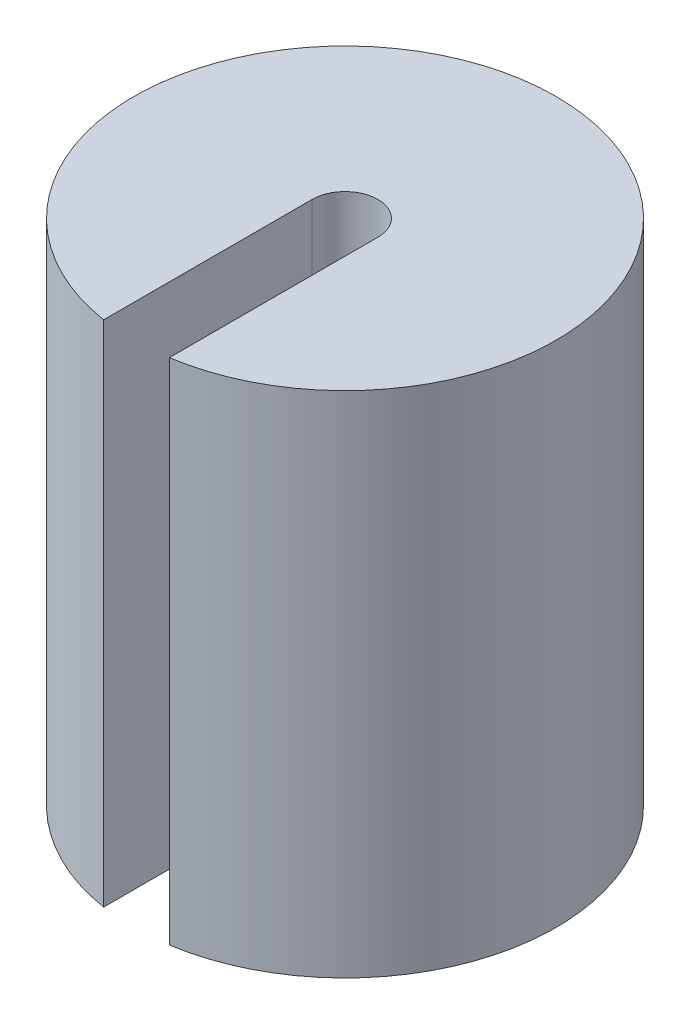
SolidWorks part; units mm, degrees
material "Brass"
ref_plane "Front Plane" through (0, 0, 0) normal (0, 0, 1) x (1, 0, 0)
ref_plane "Top Plane" through (0, 0, 0) normal (0, 1, 0) x (1, 0, 0)
ref_plane "Right Plane" through (0, 0, 0) normal (1, 0, 0) x (0, 0, -1)
sketch "Sketch1" plane through (0, 0, 0) normal (0, 1, 0) x (1, 0, 0)
  circle A0 centre (0, 0) radius 20.75
  dimension "D1" = 41.5
extrude "Boss-Extrude1" add sketch "Sketch1" along normal blind 50
sketch "Sketch2" plane through (0, 50, 0) normal (0, 1, 0) x (1, 0, 0)
  line L0 (-3.225, 0) -> (-3.225, -23.1258)
  line L1 (3.225, 0) -> (3.225, -23.1258)
  line L2 (-3.225, -23.1258) -> (3.225, -23.1258)
  arc A0 (3.225, 0) -> (-3.225, 0) centre (0, 0) ccw
  dimension "D1" = 6.45
  dimension "D2" = 23.1258
extrude "Cut-Extrude1" cut sketch "Sketch2" against normal blind 60.6
